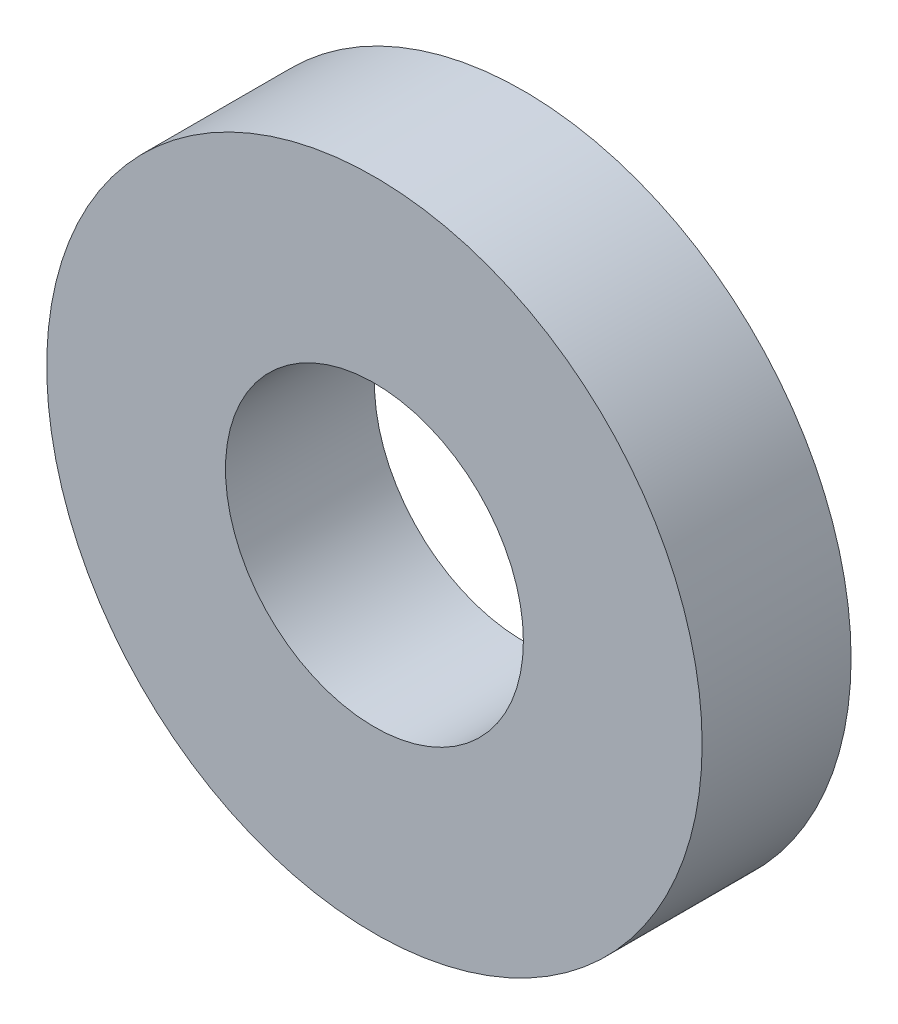
SolidWorks part; units mm, degrees
ref_plane "Front Plane" through (0, 0, 0) normal (0, 0, 1) x (1, 0, 0)
ref_plane "Top Plane" through (0, 0, 0) normal (0, 1, 0) x (1, 0, 0)
ref_plane "Right Plane" through (0, 0, 0) normal (1, 0, 0) x (0, 0, -1)
sketch "Sketch1" plane through (0, 0, 0) normal (0, 0, 1) x (1, 0, 0)
  circle A0 centre (0, 0) radius 6
  circle A1 centre (0, 0) radius 13.2
extrude "Boss-Extrude1" add sketch "Sketch1" along normal blind 6
sketch "Sketch2" plane through (0, 0, 6) normal (0, 0, 1) x (1, 0, 0)
  line L0 (0, 0) -> (0, 15.2) construction
  line L1 (-1.8199, 15.2) -> (0, 0) construction
  line L2 (1.8199, 15.2) -> (0, 0) construction
  arc A0 (-1.8199, 12) -> (1.8199, 12) centre (0, 0) cw
  arc A1 (-2.8199, 12.8953) -> (2.8199, 12.8953) centre (0, 0) cw
  arc A2 (-1.8199, 10.512) -> (1.8199, 10.512) centre (0, 0) cw
  arc A3 (-2.8199, 12.8953) -> (-1.8199, 10.512) centre (-3.5115, 11.2036) cw
  arc A4 (2.8199, 12.8953) -> (1.8199, 10.512) centre (3.5115, 11.2036) ccw
extrude "Cut-Extrude1" cut sketch "Sketch2" against normal blind 2.54 contours A1 A4 A2 A3
sketch "Sketch3" plane through (0, 0, 0) normal (0, 0, 1) x (1, 0, 0)
  circle A0 centre (0, 0) radius 6
  circle A1 centre (0, 0) radius 13.2
extrude "Boss-Extrude2" add sketch "Sketch3" along normal blind 6
